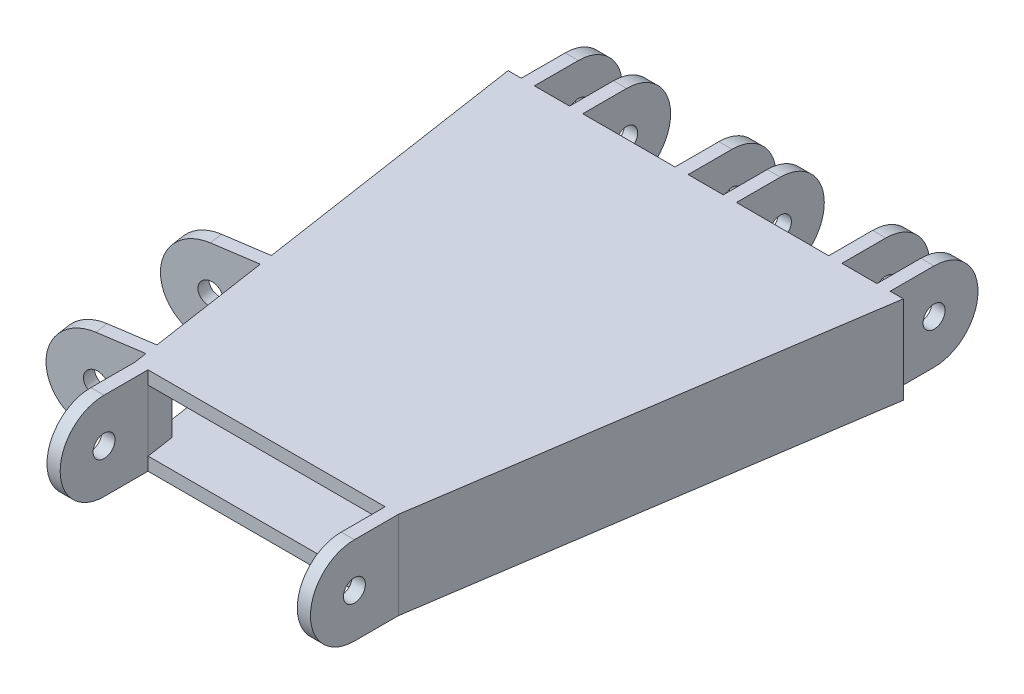
SolidWorks part; units mm, degrees
ref_plane "Front Plane" through (0, 0, 0) normal (0, 0, 1) x (1, 0, 0)
ref_plane "Top Plane" through (0, 0, 0) normal (0, 1, 0) x (1, 0, 0)
ref_plane "Right Plane" through (0, 0, 0) normal (1, 0, 0) x (0, 0, -1)
sketch "Sketch1" plane through (0, 0, 0) normal (0, 1, 0) x (1, 0, 0)
  line L0 (-45, 0) -> (45, 0)
  line L1 (45, 0) -> (30, -100)
  line L2 (30, -100) -> (-30, -100)
  line L3 (-30, -100) -> (-45, 0)
  point P2 (0, 0)
  dimension "D1" = 60
  dimension "D3" = 90
  dimension "D4" = 100
extrude "Boss-Extrude1" add sketch "Sketch1" along normal mid plane 20
sketch "Sketch2" plane through (0, 0, 0) normal (1, 0, 0) x (0, 0, -1)
  line L0 (0, 10) -> (0, -10) construction
  line L1 (0, -10) -> (-100, -10) construction
  line L2 (0, 10) -> (0, -10) construction
  line L3 (0, -10) -> (-100, -10) construction
  line L5 (0, 10) -> (10, 10)
  line L6 (0, 10) -> (0, -10)
  line L7 (0, -10) -> (10, -10)
  arc A0 (10, -10) -> (10, 10) centre (10, 0) ccw
  circle A1 centre (10, 0) radius 2.5
  dimension "D2" = 10
  dimension "D3" = 5
  dimension "D1" = 10
extrude "Boss-Extrude2" add sketch "Sketch2" along normal mid plane 14 from offset 35
pattern_linear "LPattern1" count 3 spacing 35 along (-1, 0, 0) of "Boss-Extrude2"
shell "Shell1" thickness 3
sketch "Sketch3" plane through (0, 0, 0) normal (0, 0, 1) x (1, 0, 0)
  line L0 (-42, 10) -> (-42, -10) construction
  line L1 (-42, -10) -> (-45, -10) construction
  line L2 (-45, -10) -> (-45, 10) construction
  line L3 (-45, 10) -> (-42, 10) construction
  line L4 (42, -10) -> (42, 10) construction
  line L5 (42, 10) -> (45, 10) construction
  line L6 (45, 10) -> (45, -10) construction
  line L7 (45, -10) -> (42, -10) construction
  line L8 (28, -10) -> (7, -10) construction
  line L9 (28, 10) -> (7, 10) construction
  line L10 (-7, 10) -> (-28, 10) construction
  line L11 (-7, -10) -> (-28, -10) construction
  line L12 (-45, 10) -> (-45, -10) construction
  line L13 (-42, 10) -> (-45, 10) construction
  line L14 (45, 10) -> (42, 10) construction
  line L15 (-42, 10) -> (-42, -10) construction
  line L16 (-42, -10) -> (-45, -10) construction
  line L17 (-45, -10) -> (-45, 10) construction
  line L18 (-45, 10) -> (-42, 10) construction
  line L19 (42, -10) -> (42, 10) construction
  line L20 (42, 10) -> (45, 10) construction
  line L21 (45, 10) -> (45, -10) construction
  line L22 (45, -10) -> (42, -10) construction
  line L23 (28, -10) -> (7, -10) construction
  line L24 (28, 10) -> (7, 10) construction
  line L25 (-7, 10) -> (-28, 10) construction
  line L26 (-7, -10) -> (-28, -10) construction
  line L27 (-45, 10) -> (-45, -10) construction
  line L28 (-42, 10) -> (-45, 10) construction
  line L29 (45, 10) -> (42, 10) construction
  line L31 (42, 10) -> (28, 10) construction
  line L32 (42, 10) -> (42, -10) construction
  line L33 (42, -10) -> (28, -10) construction
  line L34 (28, 10) -> (28, -10) construction
  line L35 (7, 10) -> (-7, 10) construction
  line L36 (7, 10) -> (7, -10) construction
  line L37 (7, -10) -> (-7, -10) construction
  line L38 (-7, 10) -> (-7, -10) construction
  line L39 (-28, 10) -> (-42, 10) construction
  line L40 (-28, 10) -> (-28, -10) construction
  line L41 (-28, -10) -> (-42, -10) construction
  line L42 (-42, 10) -> (-42, -10) construction
  line L43 (39, 10) -> (31, 10)
  line L44 (39, 10) -> (39, -10)
  line L45 (39, -10) -> (31, -10)
  line L46 (31, 10) -> (31, -10)
  line L47 (4, 10) -> (-4, 10)
  line L48 (4, 10) -> (4, -10)
  line L49 (4, -10) -> (-4, -10)
  line L50 (-4, 10) -> (-4, -10)
  line L51 (-31, 10) -> (-39, 10)
  line L52 (-31, 10) -> (-31, -10)
  line L53 (-31, -10) -> (-39, -10)
  line L54 (-39, 10) -> (-39, -10)
  dimension "D1" = 3
  dimension "D2" = 3
  dimension "D3" = 3
  dimension "D4" = 3
  dimension "D5" = 3
  dimension "D6" = 3
extrude "Cut-Extrude1" cut sketch "Sketch3" against normal blind 20
ref_plane "thumb plane" through (14.0098, 0, 93.3985) normal (-0.1483, 0, -0.9889) x (-0.9889, 0, 0.1483)
sketch "Sketch5" plane through (14.0098, 0, 93.3985) normal (-0.1483, 0, -0.9889) x (-0.9889, 0, 0.1483)
  line L1 (44.5021, 10) -> (44.5021, -10) construction
  line L2 (44.5021, 10) -> (44.5021, -10) construction
  line L3 (44.5021, 10) -> (54.5021, 10)
  line L4 (44.5021, 10) -> (44.5021, -10)
  line L5 (44.5021, -10) -> (54.5021, -10)
  line L6 (44.5021, 10) -> (44.5021, -10) construction
  arc A0 (54.5021, -10) -> (54.5021, 10) centre (54.5021, 0) ccw
  circle A1 centre (54.5021, 0) radius 2.5
  point P6 (44.5021, 0)
  dimension "D2" = 5
  dimension "D3" = 10
  dimension "D1" = 10
extrude "Boss-Extrude3" add sketch "Sketch5" along normal blind 3 from offset 3
pattern_linear "LPattern2" count 2 spacing 31 along (-0.1483, 0, -0.9889) of "Boss-Extrude3"
sketch "Sketch6" plane through (-44.0098, 0, 6.6015) normal (0.9889, 0, -0.1483) x (-0.1483, 0, -0.9889)
  line L0 (-88.4434, 10) -> (-88.4434, -10) construction
  line L1 (-88.4434, 7) -> (-60.4434, 7)
  line L2 (-88.4434, 7) -> (-88.4434, -7)
  line L3 (-88.4434, -7) -> (-60.4434, -7)
  line L4 (-60.4434, 7) -> (-60.4434, -7)
  line L5 (-60.4434, 10) -> (-60.4434, -10) construction
  line L6 (-103.3438, 10) -> (-6.6753, 10) construction
  line L7 (-103.3438, -10) -> (-6.6753, -10) construction
  dimension "D1" = 3
  dimension "D2" = 3
extrude "Cut-Extrude2" cut sketch "Sketch6" along normal blind 3
sketch "Sketch7" plane through (0, 0, 0) normal (1, 0, 0) x (0, 0, -1)
  line L0 (-100, 10) -> (-100, -10) construction
  line L1 (-100, 10) -> (-100, -10) construction
  line L3 (-100, 10) -> (-110, 10)
  line L4 (-100, 10) -> (-100, -10)
  line L5 (-100, -10) -> (-110, -10)
  arc A0 (-110, 10) -> (-110, -10) centre (-110, 0) ccw
  circle A1 centre (-110, 0) radius 2.5
  dimension "D2" = 5
  dimension "D1" = 10
extrude "Boss-Extrude4" add sketch "Sketch7" against normal blind 3 from offset 30
pattern_linear "LPattern3" count 2 spacing 57 along (-1, 0, 0) of "Boss-Extrude4"
